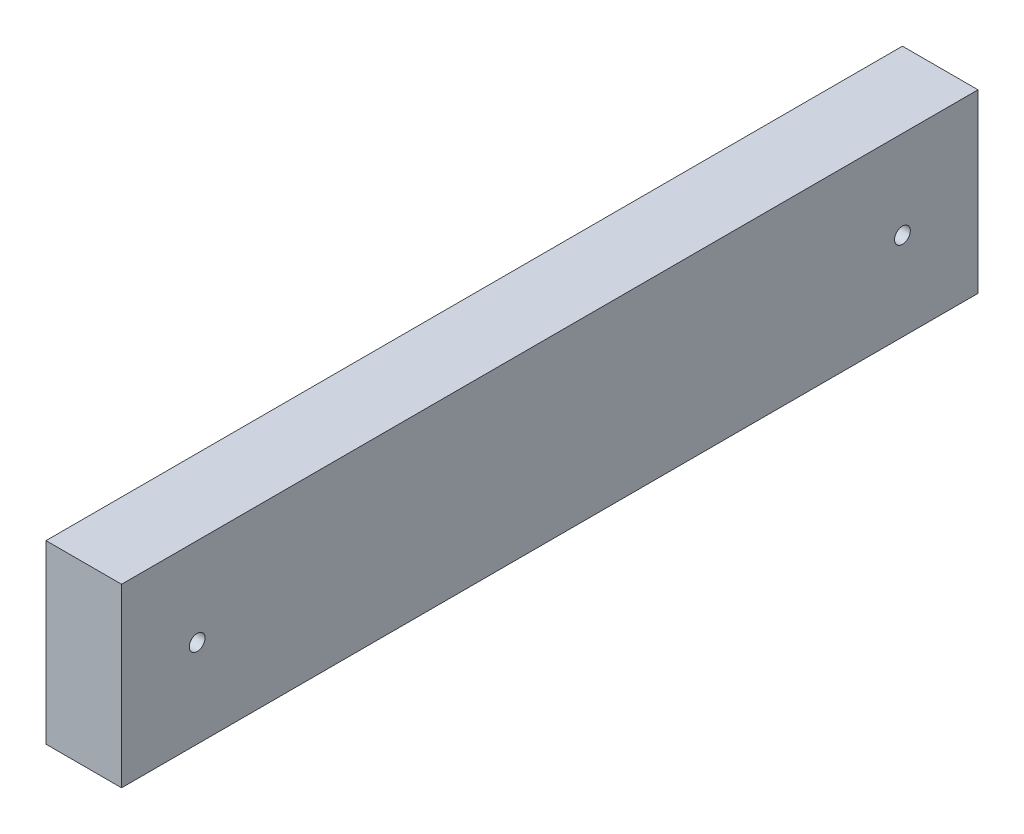
SolidWorks part; units mm, degrees
material "Pine"
ref_plane "Front Plane" through (0, 0, 0) normal (0, 0, 1) x (1, 0, 0)
ref_plane "Top Plane" through (0, 0, 0) normal (0, 1, 0) x (1, 0, 0)
ref_plane "Right Plane" through (0, 0, 0) normal (1, 0, 0) x (0, 0, -1)
sketch "Sketch1" plane through (0, 0, 0) normal (0, 0, 1) x (1, 0, 0)
  line L1 (-19.05, -44.45) -> (19.05, -44.45)
  line L2 (-19.05, -44.45) -> (-19.05, 44.45)
  line L3 (-19.05, 44.45) -> (19.05, 44.45)
  line L4 (19.05, -44.45) -> (19.05, 44.45)
  line L5 (-19.05, -44.45) -> (19.05, 44.45) construction
  line L6 (-19.05, 44.45) -> (19.05, -44.45) construction
  point P0 (0, 0)
  dimension "D1" = 88.9
  dimension "D2" = 38.1
extrude "Boss-Extrude1" add sketch "Sketch1" along normal blind 431.8
sketch "Sketch2" plane through (19.05, 0, 0) normal (1, 0, 0) x (0, 0, -1)
  line L0 (0, -44.45) -> (0, 44.45) construction
  line L1 (-431.8, -44.45) -> (-431.8, 44.45) construction
  point P0 (-393.7, 0)
  point P1 (-38.1, 0)
  dimension "D1" = 38.1
  dimension "D2" = 38.1
hole_wizard "5/16 (0.3125) Diameter Hole1" positions "Sketch3" profile "Sketch4" hole size "5/16" standard "ANSI Inch" end condition through all
sketch "Sketch3" plane through (19.05, 0, 0) normal (1, 0, 0) x (0, 0, -1)
  point P0 (-393.7, 0)
  point P3 (-38.1, 0)
sketch "Sketch4" plane through (19.05, 0, 393.7) normal (0, 1, 0) x (0, 0, -1)
  line L0 (0, 0) -> (0, 38.1)
  line L1 (0, 38.1) -> (3.9687, 38.1)
  line L2 (3.9687, 38.1) -> (3.9687, 0)
  line L5 (3.9687, 0) -> (0, 0)
  line L11 (0, -6.35) -> (0, 107.95) construction
  dimension "Thru Hole Dia." = 7.9375
  dimension "Thru Hole Depth" = 38.1
